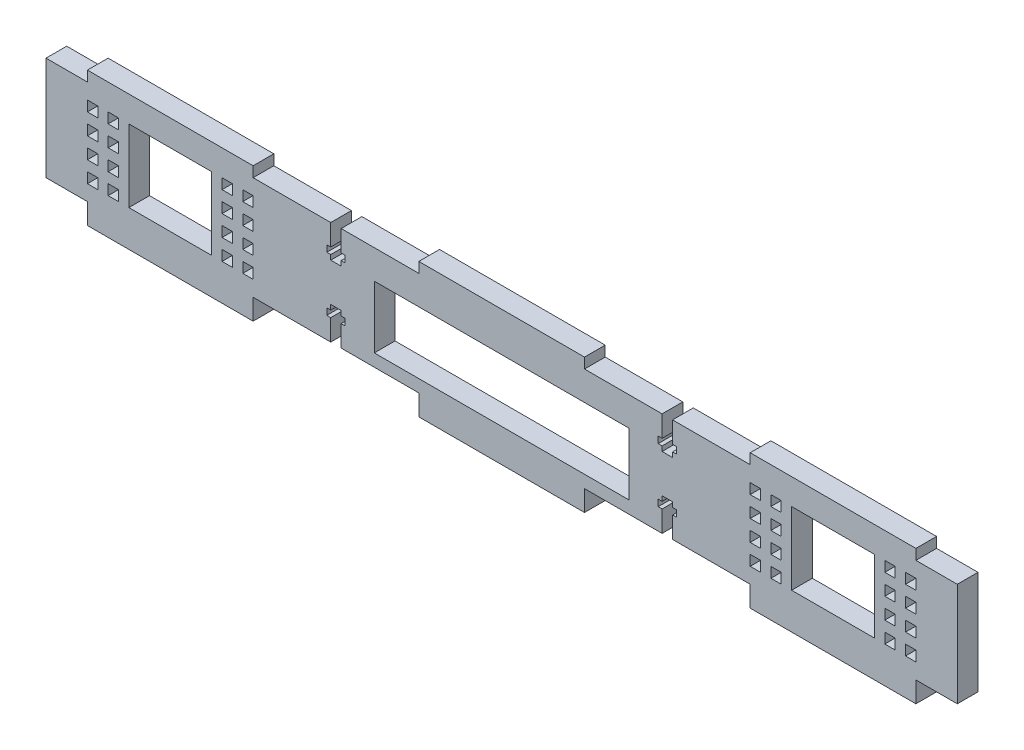
SolidWorks part; units mm, degrees
ref_plane "Front Plane" through (0, 0, 0) normal (0, 0, 1) x (1, 0, 0)
ref_plane "Top Plane" through (0, 0, 0) normal (0, 1, 0) x (1, 0, 0)
ref_plane "Right Plane" through (0, 0, 0) normal (1, 0, 0) x (0, 0, -1)
sketch "Sketch1" plane through (0, 0, 0) normal (0, 0, 1) x (1, 0, 0)
  line L0 (63.5, -3.175) -> (114.3, -3.175) construction
  line L1 (0, 0) -> (12.7, 0)
  line L2 (0, 0) -> (0, 31.75)
  line L3 (0, 31.75) -> (12.7, 31.75)
  line L4 (279.4, 0) -> (279.4, 31.75)
  line L5 (0, 15.875) -> (279.4, 15.875) construction
  line L6 (12.7, 0) -> (12.7, -6.35)
  line L7 (12.7, -6.35) -> (63.5, -6.35)
  line L8 (63.5, 0) -> (63.5, -6.35)
  line L9 (63.5, 0) -> (114.3, 0)
  line L10 (114.3, 0) -> (114.3, -6.35)
  line L11 (114.3, -6.35) -> (165.1, -6.35)
  line L12 (165.1, 0) -> (165.1, -6.35)
  line L13 (165.1, 0) -> (215.9, 0)
  line L14 (215.9, 0) -> (215.9, -6.35)
  line L15 (215.9, -6.35) -> (266.7, -6.35)
  line L16 (266.7, 0) -> (266.7, -6.35)
  line L17 (165.1, 31.75) -> (215.9, 31.75)
  line L18 (12.7, 31.75) -> (12.7, 34.925)
  line L19 (12.7, 34.925) -> (63.5, 34.925)
  line L20 (63.5, 31.75) -> (63.5, 34.925)
  line L21 (266.7, 31.75) -> (279.4, 31.75)
  line L22 (114.3, 31.75) -> (114.3, 34.925)
  line L23 (114.3, 34.925) -> (165.1, 34.925)
  line L24 (165.1, 31.75) -> (165.1, 34.925)
  line L25 (266.7, 0) -> (279.4, 0)
  line L26 (215.9, 31.75) -> (215.9, 34.925)
  line L27 (215.9, 34.925) -> (266.7, 34.925)
  line L28 (266.7, 31.75) -> (266.7, 34.925)
  line L29 (165.1, -3.175) -> (215.9, -3.175) construction
  line L30 (165.1, 33.3375) -> (215.9, 33.3375) construction
  line L31 (63.5, 33.3375) -> (114.3, 33.3375) construction
  line L32 (12.7, 33.3375) -> (0, 33.3375) construction
  line L33 (12.7, -3.175) -> (0, -3.175) construction
  line L34 (266.7, 33.3375) -> (279.4, 33.3375) construction
  line L35 (266.7, -3.175) -> (279.4, -3.175) construction
  line L36 (63.5, 31.75) -> (114.3, 31.75)
  line L37 (139.7, 34.925) -> (139.7, -6.35) construction
  line L38 (88.9, 31.75) -> (88.9, 0) construction
  dimension "D1" = 279.4
  dimension "D2" = 31.75
  dimension "D3" = 3.175
  dimension "D4" = 6.35
  dimension "D5" = 50.8
extrude "BaseExtrude" add sketch "Sketch1" along normal blind 6.35
sketch "Sketch2" plane through (0, 0, 6.35) normal (0, 0, 1) x (1, 0, 0)
  line L0 (88.9, 31.75) -> (88.9, 0) construction
  line L1 (114.3, 31.75) -> (63.5, 31.75) construction
  line L2 (63.5, 0) -> (114.3, 0) construction
  line L3 (0, 15.875) -> (279.4, 15.875) construction
  line L4 (0, 31.75) -> (0, 0) construction
  line L5 (279.4, 0) -> (279.4, 31.75) construction
  line L6 (86.1, 24.25) -> (91.7, 24.25) construction
  line L7 (90.5, 31.75) -> (87.3, 31.75)
  line L8 (90.5, 31.75) -> (90.5, 25.25)
  line L9 (90.5, 21.75) -> (87.3, 21.75)
  line L10 (87.3, 31.75) -> (87.3, 25.25)
  line L11 (86.1, 25.25) -> (87.3, 25.25)
  line L12 (86.1, 25.25) -> (86.1, 23.25)
  line L13 (86.1, 23.25) -> (87.3, 23.25)
  line L14 (86.1, 7.5) -> (91.7, 7.5) construction
  line L15 (90.5, 25.25) -> (91.7, 25.25)
  line L16 (90.5, 23.25) -> (90.5, 21.75)
  line L17 (90.5, 23.25) -> (91.7, 23.25)
  line L18 (91.7, 25.25) -> (91.7, 23.25)
  line L19 (87.3, 23.25) -> (87.3, 21.75)
  line L20 (87.3, 8.5) -> (87.3, 10)
  line L21 (91.7, 6.5) -> (91.7, 8.5)
  line L22 (90.5, 8.5) -> (91.7, 8.5)
  line L23 (90.5, 8.5) -> (90.5, 10)
  line L24 (90.5, 6.5) -> (91.7, 6.5)
  line L25 (86.1, 8.5) -> (87.3, 8.5)
  line L26 (86.1, 6.5) -> (86.1, 8.5)
  line L27 (86.1, 6.5) -> (87.3, 6.5)
  line L28 (87.3, 0) -> (87.3, 6.5)
  line L29 (90.5, 10) -> (87.3, 10)
  line L30 (90.5, 0) -> (90.5, 6.5)
  line L31 (90.5, 0) -> (87.3, 0)
  line L32 (139.7, 34.925) -> (139.7, -6.35) construction
  line L33 (165.1, 34.925) -> (114.3, 34.925) construction
  line L34 (114.3, -6.35) -> (165.1, -6.35) construction
  line L35 (193.3, 7.5) -> (187.7, 7.5) construction
  line L36 (193.3, 24.25) -> (187.7, 24.25) construction
  line L37 (188.9, 0) -> (192.1, 0)
  line L38 (188.9, 0) -> (188.9, 6.5)
  line L39 (188.9, 10) -> (192.1, 10)
  line L40 (192.1, 0) -> (192.1, 6.5)
  line L41 (193.3, 6.5) -> (192.1, 6.5)
  line L42 (193.3, 6.5) -> (193.3, 8.5)
  line L43 (193.3, 8.5) -> (192.1, 8.5)
  line L44 (188.9, 6.5) -> (187.7, 6.5)
  line L45 (188.9, 8.5) -> (188.9, 10)
  line L46 (188.9, 8.5) -> (187.7, 8.5)
  line L47 (187.7, 6.5) -> (187.7, 8.5)
  line L48 (192.1, 8.5) -> (192.1, 10)
  line L49 (192.1, 23.25) -> (192.1, 21.75)
  line L50 (187.7, 25.25) -> (187.7, 23.25)
  line L51 (188.9, 23.25) -> (187.7, 23.25)
  line L52 (188.9, 23.25) -> (188.9, 21.75)
  line L53 (188.9, 25.25) -> (187.7, 25.25)
  line L54 (193.3, 23.25) -> (192.1, 23.25)
  line L55 (193.3, 25.25) -> (193.3, 23.25)
  line L56 (193.3, 25.25) -> (192.1, 25.25)
  line L57 (192.1, 31.75) -> (192.1, 25.25)
  line L58 (188.9, 21.75) -> (192.1, 21.75)
  line L59 (188.9, 31.75) -> (188.9, 25.25)
  line L60 (188.9, 31.75) -> (192.1, 31.75)
  point P24 (88.9, 21.75)
  dimension "D1" = 2
  dimension "D2" = 5.6
  dimension "D3" = 3.2
  dimension "D4" = 10
  dimension "D5" = 7.5
extrude "ScrewCuts" cut sketch "Sketch2" against normal through all
sketch "Sketch3" plane through (0, 0, 6.35) normal (0, 0, 1) x (1, 0, 0)
  line L1 (100.66, 22.86) -> (178.74, 22.86)
  line L2 (100.66, 22.86) -> (100.66, 3.81)
  line L3 (100.66, 3.81) -> (178.74, 3.81)
  line L4 (178.74, 22.86) -> (178.74, 3.81)
  line L5 (90.5, 0) -> (114.3, 0) construction
  line L6 (188.9, 6.5) -> (188.9, 0) construction
  line L7 (25.4, 15.875) -> (12.7, 15.875) construction
  line L8 (25.4, 26.9875) -> (50.8, 26.9875)
  line L9 (25.4, 26.9875) -> (25.4, 4.7625)
  line L10 (25.4, 4.7625) -> (50.8, 4.7625)
  line L11 (50.8, 26.9875) -> (50.8, 4.7625)
  line L12 (12.7, 34.925) -> (12.7, 31.75) construction
  line L13 (63.5, 31.75) -> (63.5, 34.925) construction
  line L15 (0, 31.75) -> (0, 0) construction
  line L16 (90.5, 0) -> (90.5, 6.5) construction
  line L17 (50.8, 15.875) -> (63.5, 15.875) construction
  line L19 (139.7, 34.925) -> (139.7, -6.35) construction
  line L20 (165.1, 34.925) -> (114.3, 34.925) construction
  line L21 (114.3, -6.35) -> (165.1, -6.35) construction
  line L22 (228.6, 15.875) -> (215.9, 15.875) construction
  line L23 (254, 15.875) -> (266.7, 15.875) construction
  line L24 (228.6, 26.9875) -> (228.6, 4.7625)
  line L25 (254, 4.7625) -> (228.6, 4.7625)
  line L26 (254, 26.9875) -> (254, 4.7625)
  line L27 (254, 26.9875) -> (228.6, 26.9875)
  line L28 (50.8, 15.875) -> (63.5, 15.875) construction
  point P18 (90.5, 3.25)
  point P23 (0, 15.875)
  dimension "D1" = 10.16
  dimension "D2" = 3.81
  dimension "D3" = 10.16
  dimension "D4" = 19.05
  dimension "D5" = 22.225
  dimension "D6" = 25.4
extrude "Cut-Extrude1" cut sketch "Sketch3" against normal through all
sketch "Sketch4" plane through (0, 0, 6.35) normal (0, 0, 1) x (1, 0, 0)
  line L0 (50.8, 26.9875) -> (25.4, 26.9875) construction
  line L1 (19.05, 26.9875) -> (22.225, 26.9875)
  line L2 (19.05, 26.9875) -> (19.05, 23.8125)
  line L3 (19.05, 23.8125) -> (22.225, 23.8125)
  line L4 (22.225, 26.9875) -> (22.225, 23.8125)
  line L5 (19.05, 20.6375) -> (19.05, 17.4625)
  line L6 (12.7, 26.9875) -> (15.875, 26.9875)
  line L7 (12.7, 26.9875) -> (12.7, 23.8125)
  line L8 (12.7, 23.8125) -> (15.875, 23.8125)
  line L9 (15.875, 26.9875) -> (15.875, 23.8125)
  line L10 (25.4, 26.9875) -> (25.4, 4.7625) construction
  line L11 (22.225, 20.6375) -> (22.225, 17.4625)
  line L12 (19.05, 20.6375) -> (22.225, 20.6375)
  line L13 (19.05, 17.4625) -> (22.225, 17.4625)
  line L14 (12.7, 17.4625) -> (15.875, 17.4625)
  line L15 (15.875, 20.6375) -> (15.875, 17.4625)
  line L16 (12.7, 20.6375) -> (15.875, 20.6375)
  line L17 (12.7, 20.6375) -> (12.7, 17.4625)
  line L18 (19.05, 14.2875) -> (19.05, 11.1125)
  line L19 (22.225, 14.2875) -> (22.225, 11.1125)
  line L20 (19.05, 14.2875) -> (22.225, 14.2875)
  line L21 (19.05, 11.1125) -> (22.225, 11.1125)
  line L22 (12.7, 11.1125) -> (15.875, 11.1125)
  line L23 (15.875, 14.2875) -> (15.875, 11.1125)
  line L24 (12.7, 14.2875) -> (15.875, 14.2875)
  line L25 (12.7, 14.2875) -> (12.7, 11.1125)
  line L26 (19.05, 7.9375) -> (19.05, 4.7625)
  line L27 (22.225, 7.9375) -> (22.225, 4.7625)
  line L28 (19.05, 7.9375) -> (22.225, 7.9375)
  line L29 (19.05, 4.7625) -> (22.225, 4.7625)
  line L30 (12.7, 4.7625) -> (15.875, 4.7625)
  line L31 (15.875, 7.9375) -> (15.875, 4.7625)
  line L32 (12.7, 7.9375) -> (15.875, 7.9375)
  line L33 (12.7, 7.9375) -> (12.7, 4.7625)
  line L34 (38.1, 26.9875) -> (38.1, 4.7625) construction
  line L35 (25.4, 4.7625) -> (50.8, 4.7625) construction
  line L36 (63.5, 7.9375) -> (63.5, 4.7625)
  line L37 (63.5, 7.9375) -> (60.325, 7.9375)
  line L38 (60.325, 7.9375) -> (60.325, 4.7625)
  line L39 (63.5, 4.7625) -> (60.325, 4.7625)
  line L40 (57.15, 4.7625) -> (53.975, 4.7625)
  line L41 (57.15, 7.9375) -> (53.975, 7.9375)
  line L42 (53.975, 7.9375) -> (53.975, 4.7625)
  line L43 (57.15, 7.9375) -> (57.15, 4.7625)
  line L44 (63.5, 14.2875) -> (63.5, 11.1125)
  line L45 (63.5, 14.2875) -> (60.325, 14.2875)
  line L46 (60.325, 14.2875) -> (60.325, 11.1125)
  line L47 (63.5, 11.1125) -> (60.325, 11.1125)
  line L48 (57.15, 11.1125) -> (53.975, 11.1125)
  line L49 (57.15, 14.2875) -> (53.975, 14.2875)
  line L50 (53.975, 14.2875) -> (53.975, 11.1125)
  line L51 (57.15, 14.2875) -> (57.15, 11.1125)
  line L52 (63.5, 20.6375) -> (63.5, 17.4625)
  line L53 (63.5, 20.6375) -> (60.325, 20.6375)
  line L54 (60.325, 20.6375) -> (60.325, 17.4625)
  line L55 (63.5, 17.4625) -> (60.325, 17.4625)
  line L56 (57.15, 17.4625) -> (53.975, 17.4625)
  line L57 (57.15, 20.6375) -> (53.975, 20.6375)
  line L58 (53.975, 20.6375) -> (53.975, 17.4625)
  line L59 (60.325, 26.9875) -> (60.325, 23.8125)
  line L60 (63.5, 23.8125) -> (60.325, 23.8125)
  line L61 (63.5, 26.9875) -> (63.5, 23.8125)
  line L62 (63.5, 26.9875) -> (60.325, 26.9875)
  line L63 (57.15, 20.6375) -> (57.15, 17.4625)
  line L64 (53.975, 26.9875) -> (53.975, 23.8125)
  line L65 (57.15, 23.8125) -> (53.975, 23.8125)
  line L66 (57.15, 26.9875) -> (57.15, 23.8125)
  line L67 (57.15, 26.9875) -> (53.975, 26.9875)
  line L69 (139.7, 22.86) -> (139.7, 3.81) construction
  line L70 (178.74, 22.86) -> (100.66, 22.86) construction
  line L71 (100.66, 3.81) -> (178.74, 3.81) construction
  line L72 (222.25, 26.9875) -> (225.425, 26.9875)
  line L73 (222.25, 26.9875) -> (222.25, 23.8125)
  line L74 (222.25, 23.8125) -> (225.425, 23.8125)
  line L75 (225.425, 26.9875) -> (225.425, 23.8125)
  line L76 (222.25, 20.6375) -> (222.25, 17.4625)
  line L77 (215.9, 26.9875) -> (219.075, 26.9875)
  line L78 (215.9, 26.9875) -> (215.9, 23.8125)
  line L79 (215.9, 23.8125) -> (219.075, 23.8125)
  line L80 (219.075, 26.9875) -> (219.075, 23.8125)
  line L81 (225.425, 20.6375) -> (225.425, 17.4625)
  line L82 (222.25, 20.6375) -> (225.425, 20.6375)
  line L83 (222.25, 17.4625) -> (225.425, 17.4625)
  line L84 (215.9, 17.4625) -> (219.075, 17.4625)
  line L85 (219.075, 20.6375) -> (219.075, 17.4625)
  line L86 (215.9, 20.6375) -> (219.075, 20.6375)
  line L87 (215.9, 20.6375) -> (215.9, 17.4625)
  line L88 (222.25, 14.2875) -> (222.25, 11.1125)
  line L89 (225.425, 14.2875) -> (225.425, 11.1125)
  line L90 (222.25, 14.2875) -> (225.425, 14.2875)
  line L91 (222.25, 11.1125) -> (225.425, 11.1125)
  line L92 (215.9, 11.1125) -> (219.075, 11.1125)
  line L93 (219.075, 14.2875) -> (219.075, 11.1125)
  line L94 (215.9, 14.2875) -> (219.075, 14.2875)
  line L95 (215.9, 14.2875) -> (215.9, 11.1125)
  line L96 (222.25, 7.9375) -> (222.25, 4.7625)
  line L97 (225.425, 7.9375) -> (225.425, 4.7625)
  line L98 (222.25, 7.9375) -> (225.425, 7.9375)
  line L99 (222.25, 4.7625) -> (225.425, 4.7625)
  line L100 (215.9, 4.7625) -> (219.075, 4.7625)
  line L101 (219.075, 7.9375) -> (219.075, 4.7625)
  line L102 (215.9, 7.9375) -> (219.075, 7.9375)
  line L103 (215.9, 7.9375) -> (215.9, 4.7625)
  line L104 (266.7, 7.9375) -> (266.7, 4.7625)
  line L106 (266.7, 7.9375) -> (263.525, 7.9375)
  line L107 (263.525, 7.9375) -> (263.525, 4.7625)
  line L108 (266.7, 4.7625) -> (263.525, 4.7625)
  line L109 (260.35, 4.7625) -> (257.175, 4.7625)
  line L110 (260.35, 7.9375) -> (257.175, 7.9375)
  line L111 (257.175, 7.9375) -> (257.175, 4.7625)
  line L112 (260.35, 7.9375) -> (260.35, 4.7625)
  line L113 (266.7, 14.2875) -> (266.7, 11.1125)
  line L114 (266.7, 14.2875) -> (263.525, 14.2875)
  line L115 (263.525, 14.2875) -> (263.525, 11.1125)
  line L116 (266.7, 11.1125) -> (263.525, 11.1125)
  line L117 (260.35, 11.1125) -> (257.175, 11.1125)
  line L118 (260.35, 14.2875) -> (257.175, 14.2875)
  line L119 (257.175, 14.2875) -> (257.175, 11.1125)
  line L120 (260.35, 14.2875) -> (260.35, 11.1125)
  line L121 (266.7, 20.6375) -> (266.7, 17.4625)
  line L122 (266.7, 20.6375) -> (263.525, 20.6375)
  line L123 (263.525, 20.6375) -> (263.525, 17.4625)
  line L124 (266.7, 17.4625) -> (263.525, 17.4625)
  line L125 (260.35, 17.4625) -> (257.175, 17.4625)
  line L126 (260.35, 20.6375) -> (257.175, 20.6375)
  line L127 (257.175, 20.6375) -> (257.175, 17.4625)
  line L128 (263.525, 26.9875) -> (263.525, 23.8125)
  line L129 (266.7, 23.8125) -> (263.525, 23.8125)
  line L130 (266.7, 26.9875) -> (266.7, 23.8125)
  line L131 (266.7, 26.9875) -> (263.525, 26.9875)
  line L132 (260.35, 20.6375) -> (260.35, 17.4625)
  line L133 (257.175, 26.9875) -> (257.175, 23.8125)
  line L134 (260.35, 23.8125) -> (257.175, 23.8125)
  line L135 (260.35, 26.9875) -> (260.35, 23.8125)
  line L136 (260.35, 26.9875) -> (257.175, 26.9875)
  dimension "D1" = 3.175
  dimension "D2" = 3.175
  dimension "D3" = 2
  dimension "D4" = 4
extrude "Cut-Extrude2" cut sketch "Sketch4" against normal through all
